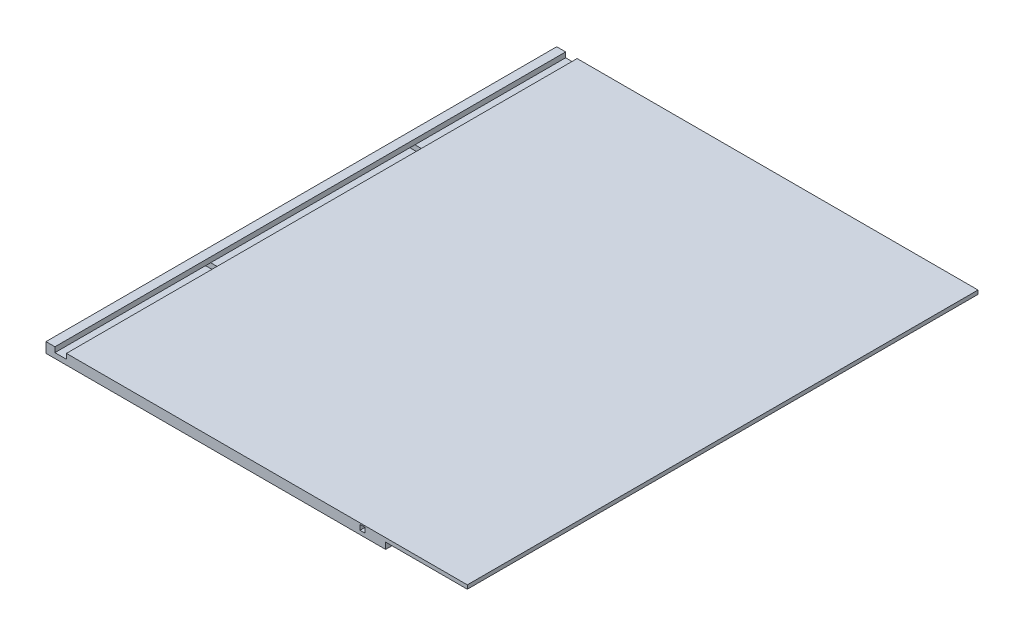
SolidWorks part; units mm, degrees
material "Polyurethane Foam Flexible"
ref_plane "Front Plane" through (0, 0, 0) normal (0, 0, 1) x (1, 0, 0)
ref_plane "Top Plane" through (0, 0, 0) normal (0, 1, 0) x (1, 0, 0)
ref_plane "Right Plane" through (0, 0, 0) normal (1, 0, 0) x (0, 0, -1)
sketch "Sketch1" plane through (0, 0, 0) normal (0, 1, 0) x (1, 0, 0)
  line L1 (-1047.75, 1270) -> (1047.75, 1270)
  line L2 (-1047.75, 1270) -> (-1047.75, -1270)
  line L3 (-1047.75, -1270) -> (1047.75, -1270)
  line L4 (1047.75, 1270) -> (1047.75, -1270)
  line L5 (-1047.75, 1270) -> (1047.75, -1270) construction
  line L6 (-1047.75, -1270) -> (1047.75, 1270) construction
  point P0 (0, 0)
  dimension "D1" = 2095.5
  dimension "D2" = 2540
extrude "Boss-Extrude1" add sketch "Sketch1" along normal blind 50.8
sketch "Sketch2" plane through (0, 0, 1270) normal (0, 0, 1) x (1, 0, 0)
  line L0 (-1047.75, 50.8) -> (-1047.75, 0) construction
  line L1 (-1003.3, 50.8) -> (-946.15, 50.8)
  line L2 (-1003.3, 50.8) -> (-1003.3, 25.4)
  line L3 (-1003.3, 25.4) -> (-946.15, 25.4)
  line L4 (-946.15, 50.8) -> (-946.15, 25.4)
  line L5 (-1003.3, 50.8) -> (-946.15, 25.4) construction
  line L6 (-1003.3, 25.4) -> (-946.15, 50.8) construction
  line L7 (-1047.75, 50.8) -> (1047.75, 50.8) construction
  line L8 (1047.75, 50.8) -> (1047.75, 0) construction
  line L9 (641.35, 31.75) -> (1047.75, 31.75)
  line L10 (641.35, 31.75) -> (641.35, 0)
  line L11 (641.35, 0) -> (1047.75, 0)
  line L12 (1047.75, 31.75) -> (1047.75, 0)
  line L13 (641.35, 31.75) -> (1047.75, 0) construction
  line L14 (641.35, 0) -> (1047.75, 31.75) construction
  line L15 (-1047.75, 0) -> (1047.75, 0) construction
  line L17 (514.35, 44.45) -> (539.75, 44.45)
  line L18 (514.35, 44.45) -> (514.35, 19.05)
  line L19 (514.35, 19.05) -> (539.75, 19.05)
  line L20 (539.75, 44.45) -> (539.75, 19.05)
  line L21 (514.35, 44.45) -> (539.75, 19.05) construction
  line L22 (514.35, 19.05) -> (539.75, 44.45) construction
  point P0 (-974.725, 38.1)
  point P9 (844.55, 15.875)
  point P18 (527.05, 31.75)
  dimension "D1" = 44.45
  dimension "D2" = 57.15
  dimension "D3" = 25.4
  dimension "D4" = 31.75
  dimension "D5" = 406.4
  dimension "D6" = 25.4
  dimension "D7" = 25.4
  dimension "D8" = 1562.1
  dimension "D9" = 19.05
extrude "Cut-Extrude1" cut sketch "Sketch2" against normal up to surface (2540 mm away) up to face at (0, 25.4, -1270)
sketch "Sketch3" plane through (-1047.75, 0, 0) normal (-1, 0, 0) x (0, 0, 1)
  line L0 (-1270, 50.8) -> (-1270, 0) construction
  line L1 (-520.7, 25.4) -> (-495.3, 25.4)
  line L2 (-520.7, 25.4) -> (-520.7, 0)
  line L3 (-520.7, 0) -> (-495.3, 0)
  line L4 (-495.3, 25.4) -> (-495.3, 0)
  line L5 (-520.7, 25.4) -> (-495.3, 0) construction
  line L6 (-520.7, 0) -> (-495.3, 25.4) construction
  line L7 (-1270, 0) -> (1270, 0) construction
  line L8 (1270, 50.8) -> (1270, 0) construction
  line L9 (495.3, 25.4) -> (520.7, 25.4)
  line L10 (495.3, 25.4) -> (495.3, 0)
  line L11 (495.3, 0) -> (520.7, 0)
  line L12 (520.7, 25.4) -> (520.7, 0)
  line L13 (495.3, 25.4) -> (520.7, 0) construction
  line L14 (495.3, 0) -> (520.7, 25.4) construction
  point P0 (-508, 12.7)
  point P9 (508, 12.7)
  dimension "D1" = 25.4
  dimension "D2" = 25.4
  dimension "D3" = 762
  dimension "D4" = 25.4
  dimension "D5" = 25.4
  dimension "D6" = 762
extrude "Cut-Extrude2" cut sketch "Sketch3" against normal up to surface (2095.5 mm away) up to face at (1047.75, 41.275, 0)
